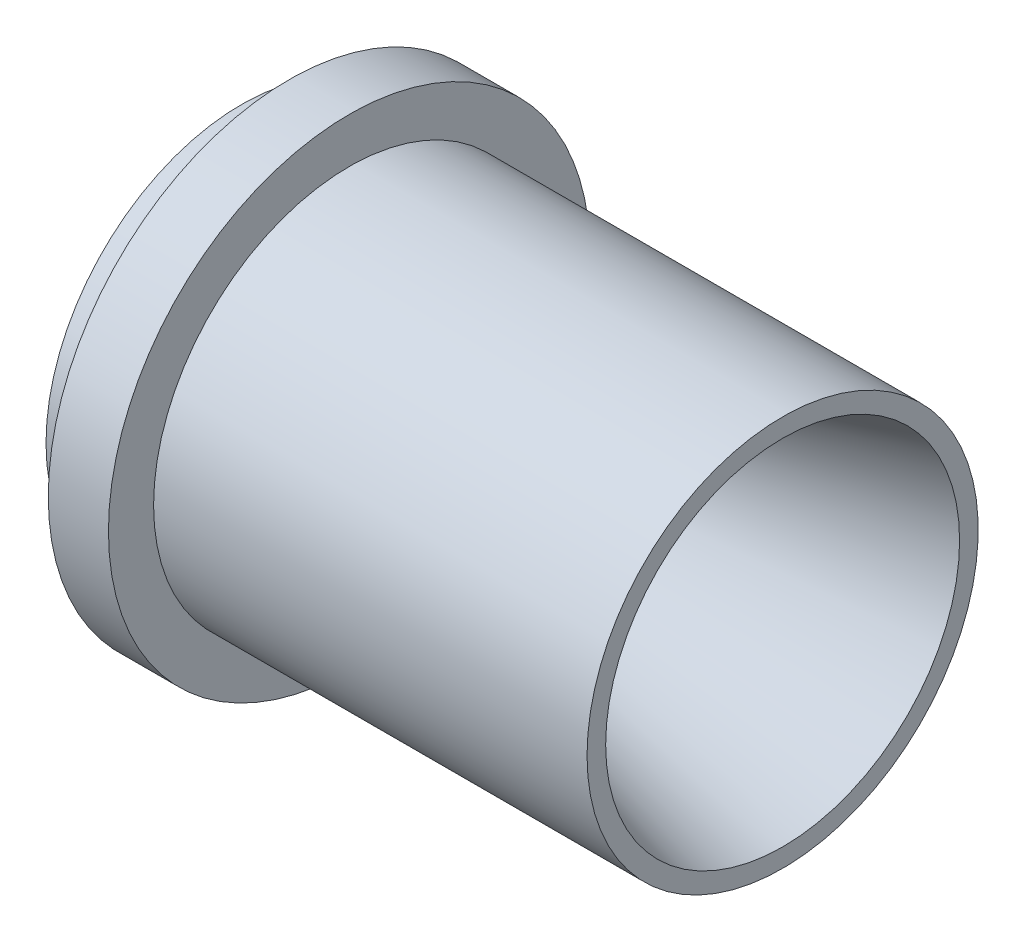
SolidWorks part; units mm, degrees
material "C (Graphite)"
ref_plane "Ebene vorne" through (0, 0, 0) normal (0, 0, 1) x (1, 0, 0)
ref_plane "Ebene oben" through (0, 0, 0) normal (0, 1, 0) x (1, 0, 0)
ref_plane "Ebene rechts" through (0, 0, 0) normal (1, 0, 0) x (0, 0, -1)
sketch "Sketch1" plane through (0, 0, 0) normal (0, 0, 1) x (1, 0, 0)
  line L0 (0, 0) -> (54.8632, 0) construction
  line L1 (-6.3, 26) -> (4.7266, 14.9734)
  line L2 (19.2155, 11.0911) -> (65.6194, 23.525)
  line L3 (-6.3, 26) -> (0, 26)
  line L5 (65.6194, 26) -> (65.6194, 23.525)
  line L6 (0, 26) -> (0, 32)
  line L8 (0, 32) -> (8, 32)
  line L9 (8, 32) -> (8, 26)
  line L10 (8, 26) -> (65.6194, 26)
  arc A0 (4.7266, 14.9734) -> (19.2155, 11.0911) centre (15.3332, 25.58) ccw
  dimension "D1" = 45
  dimension "D4" = 25.58
  dimension "D5" = 15
  dimension "D2" = 15
  dimension "D3" = 47.05
  dimension "D6" = 64
  dimension "D7" = 52
  dimension "D8" = 52
  dimension "D9" = 8
  dimension "D10" = 6.3
revolve "Revolve1" add sketch "Sketch1" angle 360 about L0
